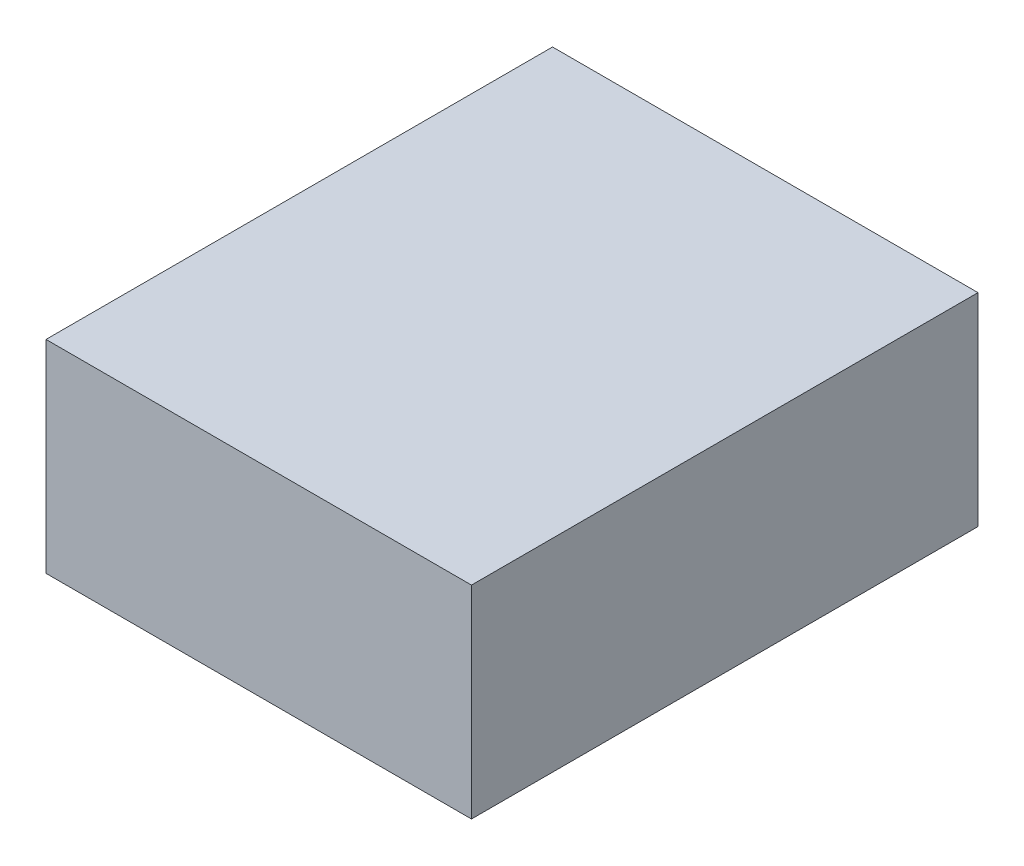
SolidWorks part; units mm, degrees
ref_plane "Front Plane" through (0, 0, 0) normal (0, 0, 1) x (1, 0, 0)
ref_plane "Top Plane" through (0, 0, 0) normal (0, 1, 0) x (1, 0, 0)
ref_plane "Right Plane" through (0, 0, 0) normal (1, 0, 0) x (0, 0, -1)
sketch "Sketch1" plane through (0, 0, 0) normal (0, 1, 0) x (1, 0, 0)
  line L1 (-0.0028, 0) -> (1.0472, 0)
  line L2 (-0.0028, 0) -> (-0.0028, 1.25)
  line L3 (-0.0028, 1.25) -> (1.0472, 1.25)
  line L4 (1.0472, 0) -> (1.0472, 1.25)
  dimension "D1" = 1.25
  dimension "D2" = 1.05
extrude "Boss-Extrude1" add sketch "Sketch1" along normal blind 0.5
